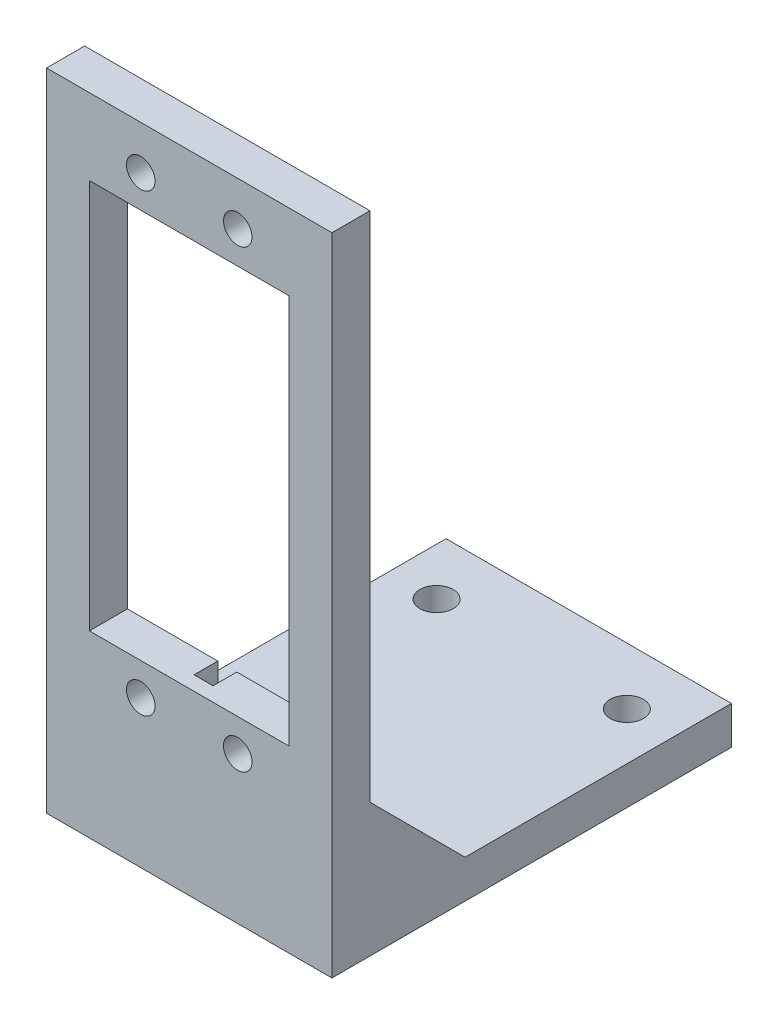
SolidWorks part; units mm, degrees
ref_plane "前基準面" through (0, 0, 0) normal (0, 0, 1) x (1, 0, 0)
ref_plane "上基準面" through (0, 0, 0) normal (0, 1, 0) x (1, 0, 0)
ref_plane "右基準面" through (0, 0, 0) normal (1, 0, 0) x (0, 0, -1)
sketch "草圖1" plane through (0, 0, 0) normal (0, 0, 1) x (1, 0, 0)
  line L0 (15, 63.8559) -> (15, 0) construction
  line L1 (0, 0) -> (30, 0)
  line L2 (0, 0) -> (0, 63.8559)
  line L3 (0, 63.8559) -> (30, 63.8559)
  line L4 (30, 0) -> (30, 63.8559)
  line L5 (4.5, 35.3559) -> (25.5, 35.3559) construction
  line L6 (4.5, 55.8559) -> (25.5, 55.8559)
  line L7 (4.5, 55.8559) -> (4.5, 14.8559)
  line L8 (4.5, 14.8559) -> (25.5, 14.8559)
  line L9 (25.5, 55.8559) -> (25.5, 14.8559)
  circle A0 centre (9.9, 59.2559) radius 1.5
  circle A1 centre (20.1, 59.2559) radius 1.5
  circle A2 centre (20.1, 11.4559) radius 1.5
  circle A3 centre (9.9, 11.4559) radius 1.5
  dimension "D6" = 3
  dimension "D7" = 5.1
  dimension "D8" = 23.9
  dimension "D1" = 30
  dimension "D2" = 21
  dimension "D3" = 10.5
  dimension "D4" = 41
  dimension "D5" = 8
extrude "填料-伸長1" add sketch "草圖1" along normal blind 4
sketch "草圖2" plane through (0, 0, 0) normal (0, 0, -1) x (-1, 0, 0)
  line L0 (-15, 63.8559) -> (-15, 0) construction
  line L1 (-30, 63.8559) -> (0, 63.8559) construction
  line L2 (0, 0) -> (-30, 0) construction
  line L3 (-25.5, 55.8559) -> (-4.5, 55.8559) construction
  line L4 (-16, 58.8559) -> (-14, 58.8559)
  line L5 (-16, 58.8559) -> (-16, 55.8559)
  line L6 (-16, 55.8559) -> (-14, 55.8559)
  line L7 (-14, 58.8559) -> (-14, 55.8559)
  line L8 (-4.5, 14.8559) -> (-25.5, 14.8559) construction
  line L9 (-16, 14.8559) -> (-14, 14.8559)
  line L10 (-16, 14.8559) -> (-16, 11.8559)
  line L11 (-16, 11.8559) -> (-14, 11.8559)
  line L12 (-14, 14.8559) -> (-14, 11.8559)
  dimension "D1" = 1
  dimension "D2" = 1
  dimension "D3" = 1
  dimension "D4" = 1
  dimension "D5" = 3
  dimension "D6" = 3
extrude "除料-伸長1" cut sketch "草圖2" against normal blind 2.5
sketch "草圖3" plane through (0, 0, 0) normal (0, -1, 0) x (1, 0, 0)
  line L0 (30, 4) -> (30, 0) construction
  line L1 (0, 4) -> (30, 4)
  line L2 (0, 4) -> (0, -38)
  line L3 (0, -38) -> (30, -38)
  line L4 (30, 4) -> (30, -38)
  dimension "D1" = 42
extrude "填料-伸長2" add sketch "草圖3" along normal blind 4
sketch "草圖4" plane through (0, 0, 0) normal (0, 1, 0) x (1, 0, 0)
  line L0 (15, 38) -> (15, -4) construction
  line L1 (0, 38) -> (30, 38) construction
  line L2 (30, -4) -> (0, -4) construction
  line L3 (0, 0) -> (30, 0) construction
  circle A0 centre (5, 32) radius 1.75
  circle A1 centre (25, 32) radius 1.75
  dimension "D1" = 10
  dimension "D2" = 3.5
  dimension "D3" = 32
extrude "除料-伸長2" cut sketch "草圖4" against normal through all
sketch "草圖5" plane through (30, 0, 0) normal (1, 0, 0) x (0, 0, -1)
  line L0 (0, 10) -> (10, 0)
  line L1 (38, 0) -> (0, 0) construction
  line L2 (10, 0) -> (0, 0)
  line L3 (0, 0) -> (0, 10)
  line L4 (0, 0) -> (0, 63.8559) construction
  dimension "D1" = 10
  dimension "D2" = 10
extrude "填料-伸長3" add sketch "草圖5" against normal blind 3
sketch "草圖6" plane through (0, 0, 0) normal (-1, 0, 0) x (0, 0, 1)
  line L0 (0, 0) -> (0, 10)
  line L1 (0, 10) -> (-10, 0)
  line L2 (-10, 0) -> (0, 0)
extrude "填料-伸長4" add sketch "草圖6" against normal blind 3
